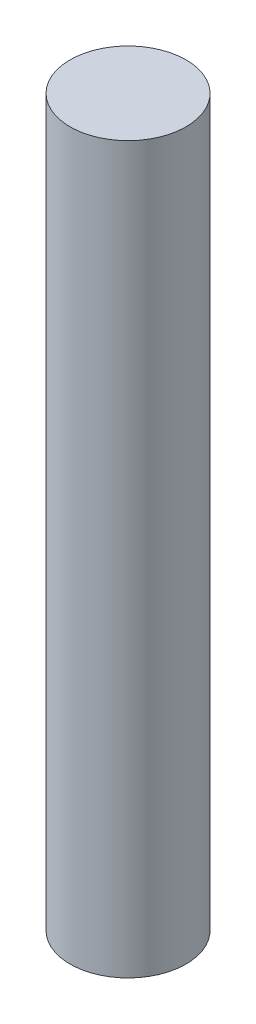
SolidWorks part; units mm, degrees
ref_plane "Plan de face" through (0, 0, 0) normal (0, 0, 1) x (1, 0, 0)
ref_plane "Plan de dessus" through (0, 0, 0) normal (0, 1, 0) x (1, 0, 0)
ref_plane "Plan de droite" through (0, 0, 0) normal (1, 0, 0) x (0, 0, -1)
sketch "Esquisse1" plane through (0, 0, 0) normal (0, 0, 1) x (1, 0, 0)
  line L0 (2.5, 0) -> (4, 0)
  line L1 (4, 0) -> (4, 50)
  line L2 (4, 50) -> (0, 50)
  line L3 (2.5, 0) -> (2.5, 10)
  line L4 (2.5, 10) -> (0, 10)
  line L5 (0, 10) -> (0, 50) construction
  line L6 (0, 50) -> (0, 10)
revolve "Révolution1" add sketch "Esquisse1" angle 360 about L5
